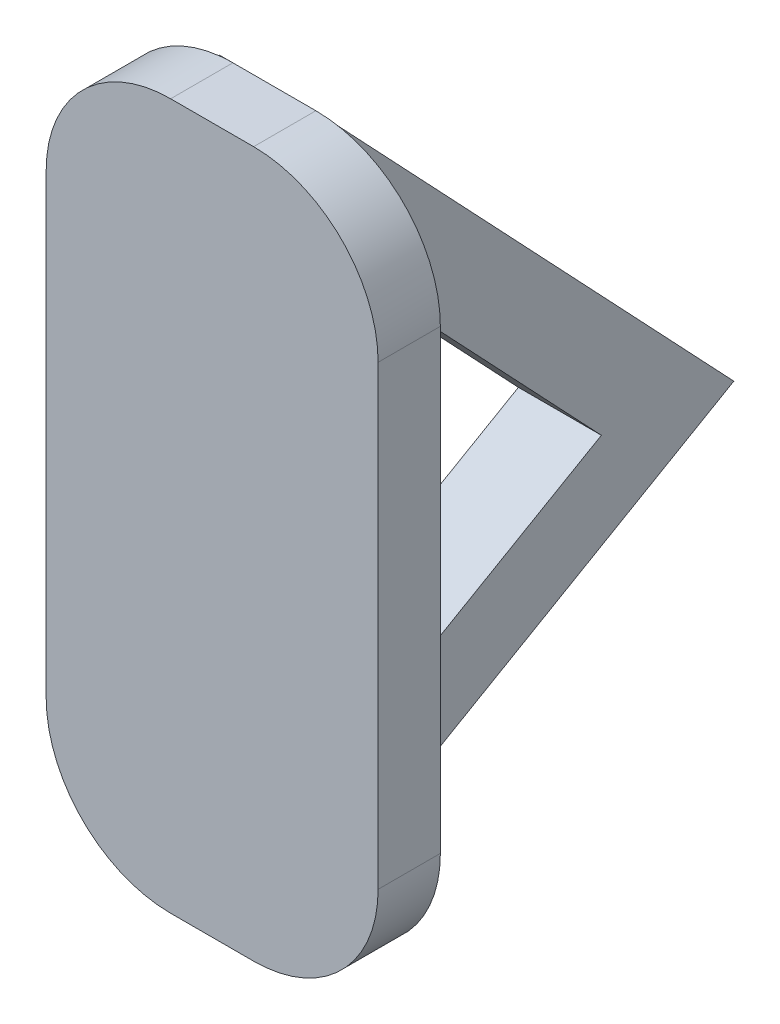
SolidWorks part; units mm, degrees
ref_plane "Front Plane" through (0, 0, 0) normal (0, 0, 1) x (1, 0, 0)
ref_plane "Top Plane" through (0, 0, 0) normal (0, 1, 0) x (1, 0, 0)
ref_plane "Right Plane" through (0, 0, 0) normal (1, 0, 0) x (0, 0, -1)
sketch "Sketch1" plane through (0, 0, 0) normal (0, 0, 1) x (1, 0, 0)
  line L1 (-1, 8.5) -> (1, 8.5)
  line L2 (-4, 5.5) -> (-4, -5.5)
  line L3 (-1, -8.5) -> (1, -8.5)
  line L4 (4, 5.5) -> (4, -5.5)
  line L5 (-4, 8.5) -> (4, -8.5) construction
  line L6 (-4, -8.5) -> (4, 8.5) construction
  arc A0 (1, -8.5) -> (4, -5.5) centre (1, -5.5) ccw
  arc A1 (-1, -8.5) -> (-4, -5.5) centre (-1, -5.5) cw
  arc A2 (4, 5.5) -> (1, 8.5) centre (1, 5.5) ccw
  arc A3 (-1, 8.5) -> (-4, 5.5) centre (-1, 5.5) ccw
  point P0 (0, 0)
  dimension "D3" = 3
  dimension "D1" = 8
  dimension "D2" = 17
extrude "Boss-Extrude1" add sketch "Sketch1" along normal blind 1.5
sketch "Sketch3" plane through (0, 0, 0) normal (0, 0, -1) x (-1, 0, 0)
  line L0 (-1, 8.5) -> (1, 8.5) construction
  line L1 (-0.6802, 8.5) -> (1.3198, 8.5)
  line L2 (-0.6802, 8.5) -> (-0.6802, -8.5)
  line L3 (-0.6802, -8.5) -> (1.3198, -8.5)
  line L4 (1.3198, 8.5) -> (1.3198, -8.5)
  line L5 (1, -8.5) -> (-1, -8.5) construction
  dimension "D1" = 2
extrude "Boss-Extrude2" add sketch "Sketch3" along normal blind 20
sketch "Sketch4" plane through (0.6802, 0, 0) normal (1, 0, 0) x (0, 0, -1)
  line L0 (0, -8.5) -> (10.3923, -2.5)
  line L1 (10.3923, -2.5) -> (0, 8.5)
  line L2 (20, -8.5) -> (0, -8.5) construction
  line L3 (20, 8.5) -> (0, 8.5) construction
  line L4 (20, 8.5) -> (0, 8.5)
  line L5 (20, 8.5) -> (20, -8.5) construction
  line L6 (20, 8.5) -> (20, -8.5)
  line L7 (20, -8.5) -> (0, -8.5)
  dimension "D1" = 30
  dimension "D2" = 12
  dimension "D3" = 15.1327
extrude "Cut-Extrude1" cut sketch "Sketch4" against normal through all
sketch "Sketch5" plane through (0.6802, 0, 0) normal (1, 0, 0) x (0, 0, -1)
  line L9 (2, 3.4708) -> (2, -5.0359)
  line L10 (2, -5.0359) -> (7.2002, -2.0336)
  line L11 (7.2002, -2.0336) -> (2, 3.4708)
  line L12 (2, 3.4708) -> (2, -5.0359)
  line L13 (2, -5.0359) -> (7.2002, -2.0336)
  line L14 (7.2002, -2.0336) -> (2, 3.4708)
  dimension "D1" = 2
extrude "Cut-Extrude2" cut sketch "Sketch5" against normal through all
